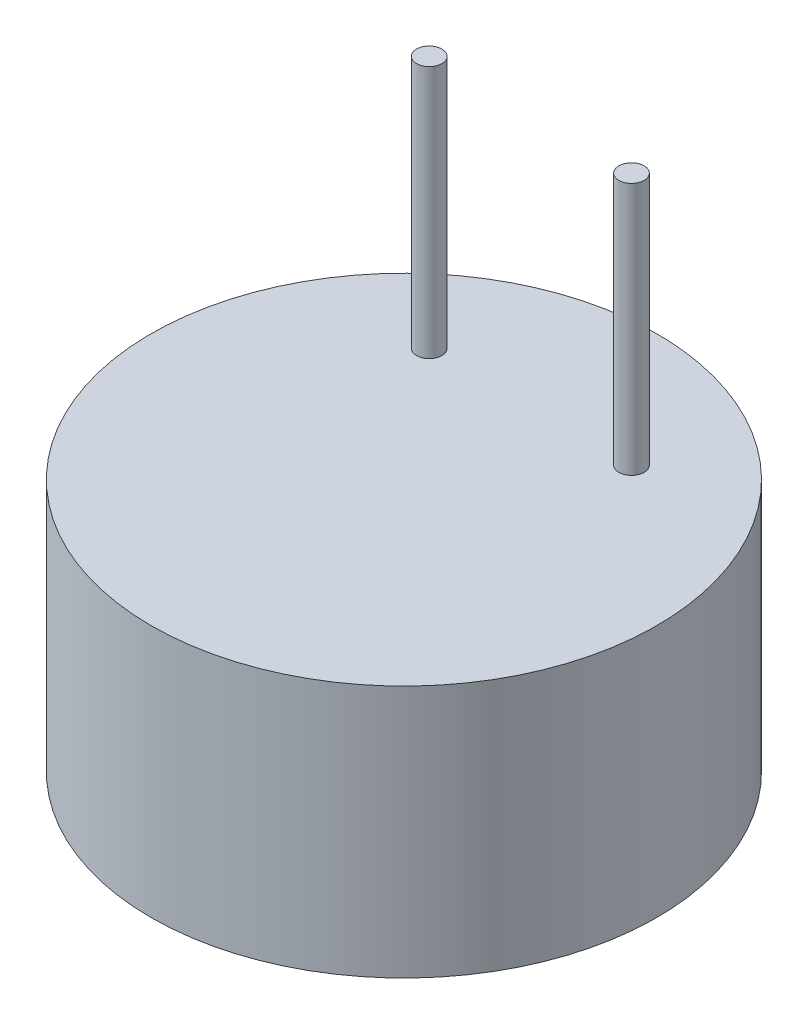
SolidWorks part; units mm, degrees
ref_plane "Front Plane" through (0, 0, 0) normal (0, 0, 1) x (1, 0, 0)
ref_plane "Top Plane" through (0, 0, 0) normal (0, 1, 0) x (1, 0, 0)
ref_plane "Right Plane" through (0, 0, 0) normal (1, 0, 0) x (0, 0, -1)
sketch "Sketch1" plane through (0, 0, 0) normal (0, 1, 0) x (1, 0, 0)
  circle A0 centre (0, 0) radius 5
  dimension "D1" = 10
extrude "Boss-Extrude1" add sketch "Sketch1" along normal blind 5 contours A0
sketch "Sketch2" plane through (0, 5, 0) normal (0, 1, 0) x (1, 0, 0)
  line L0 (-4.3301, 2.5) -> (4.3301, 2.5) construction
  line L1 (0, 5) -> (0, 0) construction
  circle A0 centre (0, 0) radius 5 construction
  circle A1 centre (-2, 2.5) radius 0.25
  circle A2 centre (2, 2.5) radius 0.25
  dimension "D2" = 2
  dimension "D3" = 0.5
  dimension "D1" = 2.5
extrude "Boss-Extrude2" add sketch "Sketch2" along normal blind 5
